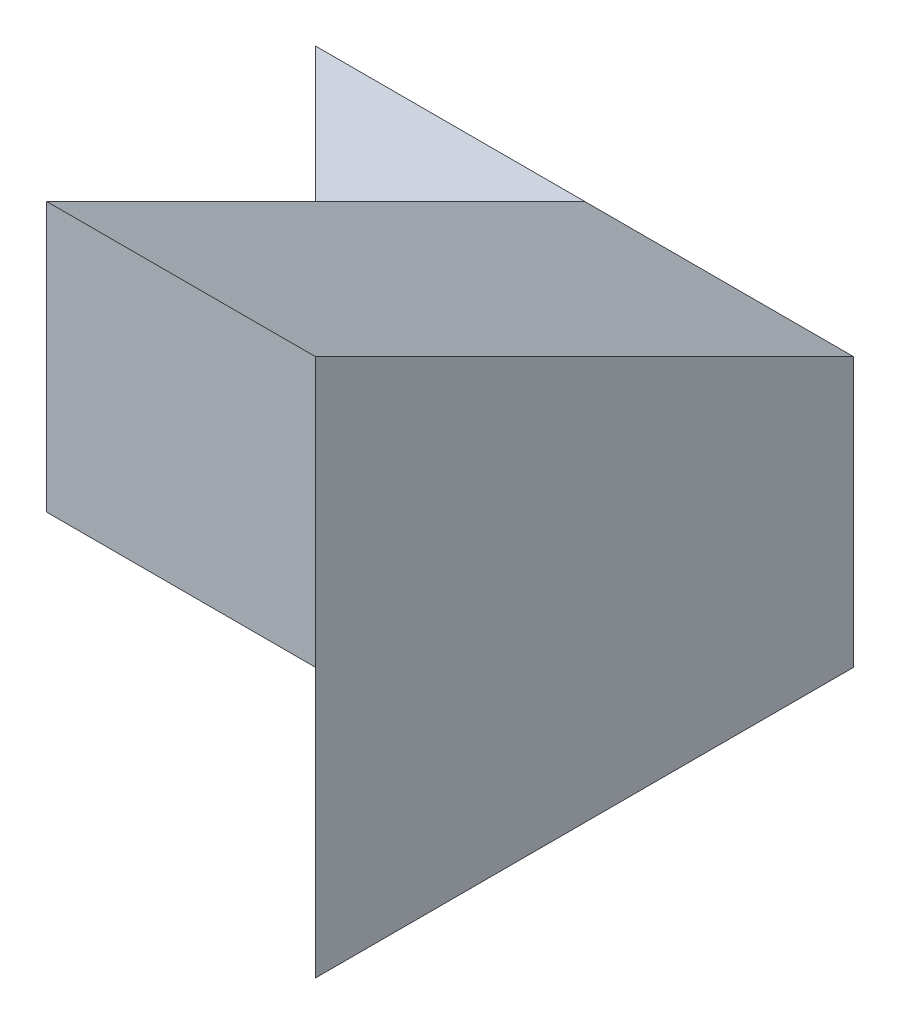
SolidWorks part; units mm, degrees
ref_plane "Front Plane" through (0, 0, 0) normal (0, 0, 1) x (1, 0, 0)
ref_plane "Top Plane" through (0, 0, 0) normal (0, 1, 0) x (1, 0, 0)
ref_plane "Right Plane" through (0, 0, 0) normal (1, 0, 0) x (0, 0, -1)
sketch "Sketch1" plane through (0, 0, 0) normal (0, 0, 1) x (1, 0, 0)
  line L1 (0, 0) -> (40, 0)
  line L2 (0, 0) -> (0, 40)
  line L3 (0, 40) -> (40, 40)
  line L4 (40, 0) -> (40, 40)
  dimension "D1" = 40
  dimension "D2" = 40
extrude "Boss-Extrude1" add sketch "Sketch1" along normal blind 40
sketch "Sketch2" plane through (0, 0, 40) normal (0, 0, 1) x (1, 0, 0)
  line L1 (0, 40) -> (20, 40)
  line L2 (0, 40) -> (0, 20)
  line L3 (0, 20) -> (20, 20)
  line L4 (20, 40) -> (20, 20)
  dimension "D1" = 20
  dimension "D2" = 20
extrude "Cut-Extrude1" cut sketch "Sketch2" against normal blind 40
sketch "Sketch3" plane through (20, 0, 0) normal (-1, 0, 0) x (0, 0, 1)
  line L0 (0, 20) -> (40, 40)
  line L1 (40, 40) -> (0, 40)
  line L2 (0, 40) -> (0, 20)
extrude "Cut-Extrude2" cut sketch "Sketch3" against normal blind 40
sketch "Sketch4" plane through (0, 0, 0) normal (0, 1, 0) x (1, 0, 0)
  line L0 (0, 0) -> (20, -20)
  line L1 (20, 0) -> (20, -40) construction
  line L2 (20, -20) -> (20, -40)
  line L3 (20, -40) -> (0, -40)
  line L4 (0, -40) -> (0, 0)
extrude "Cut-Extrude6" cut sketch "Sketch4" along normal blind 40
sketch "Sketch6" plane through (0, 0, 0) normal (0, -1, 0) x (-1, 0, 0)
  line L0 (-20.001, -39.9999) -> (-39.999, -39.9999)
  line L1 (-39.999, -39.9999) -> (-20.001, -20.0019)
  line L2 (-20.001, -20.0019) -> (-20.001, -39.9999)
  line L3 (-20, -20) -> (0, 0) construction
  line L4 (-20, -40) -> (-40, -40) construction
  point P7 (-38.0809, -39.1372)
  dimension "D1" = 19.998
  dimension "D2" = 0.001
  dimension "D3" = 0.0001
extrude "Cut-Extrude7" cut sketch "Sketch6" against normal blind 19.999
sketch "Sketch7" plane through (20.001, 0, 0) normal (1, 0, 0) x (0, 0, -1)
  line L0 (-39.9999, 0) -> (-20.0019, 0)
  line L1 (-20.0019, 0) -> (-20.0019, 19.999)
  line L2 (-20.0019, 19.999) -> (-39.9999, 19.999)
  line L3 (-39.9999, 19.999) -> (-39.9999, 0)
extrude "Cut-Extrude8" cut sketch "Sketch7" against normal blind 19.999
sketch "Sketch8" plane through (0, 0, 39.9999) normal (0, 0, -1) x (-1, 0, 0)
  line L1 (-39.999, 19.999) -> (-20, 19.999)
  line L2 (-39.999, 19.999) -> (-39.999, 0)
  line L3 (-39.999, 0) -> (-20, 0)
  line L4 (-20, 19.999) -> (-20, 0)
extrude "Cut-Extrude9" cut sketch "Sketch8" against normal blind 19.999
sketch "Sketch11" plane through (-0.0005, 0, 0.0005) normal (-0.7071, 0, 0.7071) x (0.7071, 0, 0.7071)
  line L0 (28.2863, 19.999) -> (56.5678, 19.999) construction
  line L1 (28.2863, 19.999) -> (56.5678, 19.999)
  line L2 (28.2863, 19.999) -> (28.2863, 0)
  line L3 (28.2863, 0) -> (56.5678, 0)
  line L4 (56.5678, 19.999) -> (56.5678, 0)
  line L5 (28.2863, 19.999) -> (28.2863, 0) construction
extrude "Boss-Extrude9" add sketch "Sketch11" along normal blind 0.0009
sketch "Sketch13" plane through (0, 0, 0) normal (0, -1, 0) x (-1, 0, 0)
  line L0 (-20.0004, -20.0025) -> (-20, -20.0019)
  line L1 (-20, -20.0019) -> (-20.001, -20.0019)
  line L2 (-20.001, -20.0019) -> (-20.0004, -20.0025)
extrude "Boss-Extrude10" add sketch "Sketch13" against normal blind 20
sketch "Sketch14" plane through (0, 0, 0) normal (-0.7071, 0, 0.7071) x (0.7071, 0, 0.7071)
  line L1 (0, 20) -> (57, 20)
  line L2 (0, 20) -> (0, 0)
  line L3 (0, 0) -> (57, 0)
  line L4 (57, 20) -> (57, 0)
  dimension "D1" = 20
  dimension "D2" = 57
extrude "Cut-Extrude11" cut sketch "Sketch14" along normal blind 20
